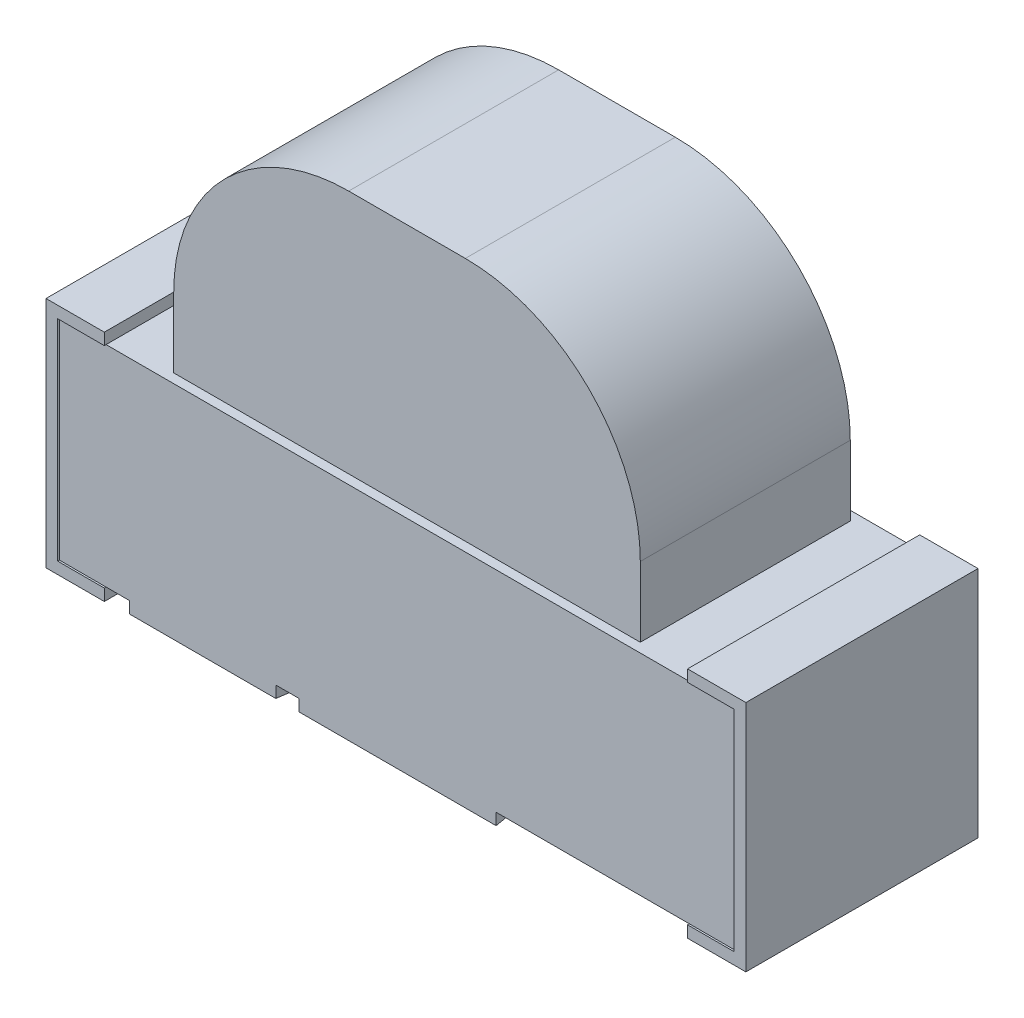
SolidWorks part; units mm, degrees
ref_plane "Vorne" through (0, 0, 0) normal (0, 0, 1) x (1, 0, 0)
ref_plane "Oben" through (0, 0, 0) normal (0, 1, 0) x (1, 0, 0)
ref_plane "Rechts" through (0, 0, 0) normal (1, 0, 0) x (0, 0, -1)
sketch "Skizze1" plane through (0, 0, 0) normal (0, 1, 0) x (1, 0, 0)
  line L0 (-1.45, -0.49) -> (1.45, 0.49) construction
  line L1 (-1.45, 0.49) -> (1.45, 0.49)
  line L2 (-1.45, 0.49) -> (-1.45, -0.49)
  line L3 (-1.45, -0.49) -> (1.45, -0.49)
  line L4 (1.45, 0.49) -> (1.45, -0.49)
  line L5 (1.45, -0.49) -> (-1.45, 0.49) construction
  dimension "D1" = 0.98
  dimension "D2" = 2.9
extrude "Linear austragen1" add sketch "Skizze1" along normal blind 0.9
sketch "Skizze2" plane through (0, 0, 0) normal (0, 0, 1) x (1, 0, 0)
  line L0 (-1.45, 0.9) -> (1.45, 0.9) construction
  line L1 (-1, 0.9) -> (1, 0.9)
  line L2 (-1, 0.9) -> (-1, 1.2)
  line L3 (-0.25, 1.95) -> (0.25, 1.95)
  line L4 (1, 0.9) -> (1, 1.2)
  line L7 (0, 0) -> (0, 0.9) construction
  arc A0 (0.25, 1.95) -> (1, 1.2) centre (0.25, 1.2) cw
  arc A1 (-1, 1.2) -> (-0.25, 1.95) centre (-0.25, 1.2) cw
  point P11 (1, 1.95)
  point P14 (-1, 1.95)
  dimension "D3" = 0.75
  dimension "D1" = 1.05
  dimension "D2" = 2
extrude "Linear austragen2" add sketch "Skizze2" against normal mid plane 0.9 separate body
sketch "Skizze5" plane through (0, 0.9, 0) normal (0, 1, 0) x (1, 0, 0)
  line L10 (-1.45, 0.49) -> (-1.45, -0.49) construction
  line L11 (-1.45, -0.49) -> (1.45, -0.49) construction
  line L12 (1.45, -0.49) -> (1.45, 0.49) construction
  line L13 (1.45, 0.49) -> (-1.45, 0.49) construction
  line L14 (-1.5, 0.54) -> (-1.5, -0.54)
  line L15 (-1.5, -0.54) -> (1.5, -0.54)
  line L16 (1.5, -0.54) -> (1.5, 0.54)
  line L17 (1.5, 0.54) -> (-1.5, 0.54)
  line L18 (-1.5, 0.54) -> (-1.5, -0.54)
  line L19 (-1.5, -0.54) -> (1.5, -0.54)
  line L20 (1.5, -0.54) -> (1.5, 0.54)
  line L21 (1.5, 0.54) -> (-1.5, 0.54)
  line L22 (-1.45, 0.49) -> (-1.45, -0.49)
  line L23 (-1.45, -0.49) -> (1.45, -0.49)
  line L24 (1.45, -0.49) -> (1.45, 0.49)
  line L25 (1.45, 0.49) -> (-1.45, 0.49)
  dimension "D1" = 0.05
extrude "Linear austragen6" add sketch "Skizze5" against normal up to surface (0.9 mm away) separate body up to face at (0, 0, 0)
sketch "Skizze6" plane through (0, 0.9, 0) normal (0, 1, 0) x (1, 0, 0)
  line L0 (1.5, -0.54) -> (-1.5, -0.54) construction
  line L1 (1.25, 0.54) -> (1.25, -0.54)
  line L2 (1.5, 0.54) -> (-1.5, 0.54) construction
  line L5 (-1.5, -0.54) -> (1.5, -0.54) construction
  line L6 (1.25, -0.54) -> (1.5, -0.54)
  line L7 (0, -0.54) -> (0, 0) construction
  line L8 (1.5, -0.54) -> (1.5, 0.54)
  line L9 (1.5, 0.54) -> (1.25, 0.54)
  line L10 (-1.5, 0.54) -> (-1.25, 0.54)
  line L11 (-1.5, -0.54) -> (-1.5, 0.54)
  line L12 (-1.25, -0.54) -> (-1.5, -0.54)
  line L13 (-1.25, 0.54) -> (-1.25, -0.54)
  dimension "D1" = 0.25
extrude "Linear austragen7" add sketch "Skizze6" along normal blind 0.05
sketch "Skizze7" plane through (0, 0, 0) normal (0, -1, 0) x (1, 0, 0)
  line L0 (1.5, -0.54) -> (1.25, -0.54) construction
  line L1 (1.5, 0.54) -> (1.5, -0.54) construction
  line L2 (1.25, 0.54) -> (1.5, 0.54) construction
  line L3 (1.25, -0.54) -> (1.25, 0.54) construction
  line L4 (1.5, -0.54) -> (1.25, -0.54)
  line L5 (1.5, 0.54) -> (1.5, -0.54)
  line L6 (1.25, 0.54) -> (1.5, 0.54)
  line L7 (1.25, -0.54) -> (1.25, 0.54)
  line L8 (0, 0) -> (0, 0.54) construction
  line L9 (1.5, 0.54) -> (-1.5, 0.54) construction
  line L10 (-1.25, -0.54) -> (-1.25, 0.54)
  line L11 (-1.25, 0.54) -> (-1.5, 0.54)
  line L12 (-1.5, 0.54) -> (-1.5, -0.54)
  line L13 (-1.5, -0.54) -> (-1.25, -0.54)
extrude "Linear austragen8" add sketch "Skizze7" along normal blind 0.05
sketch "Skizze8" plane through (0, 0, 0) normal (0, -1, 0) x (1, 0, 0)
  line L0 (0, 0.54) -> (0, -0.54) construction
  line L1 (1.25, 0.54) -> (-1.25, 0.54) construction
  line L2 (-1.25, -0.54) -> (1.25, -0.54) construction
  line L3 (0, 0) -> (1.5, 0) construction
  line L4 (1.5, -0.54) -> (1.5, 0.54) construction
  line L5 (-0.125, 0.1338) -> (-0.125, -0.1338)
  line L6 (0.125, 0.1338) -> (0.125, -0.1338)
  line L7 (-0.425, 0.54) -> (0.425, 0.54)
  line L8 (0.425, -0.54) -> (-0.425, -0.54)
  line L9 (-0.225, 0.0657) -> (-0.225, -0.0657)
  line L11 (-1.15, 0.54) -> (-0.525, 0.54)
  line L12 (-1.15, -0.54) -> (-1.15, 0.54)
  line L13 (-1.15, -0.54) -> (-1.15, 0.54)
  line L14 (-0.525, -0.54) -> (-1.15, -0.54)
  arc A0 (-0.425, 0.54) -> (-0.125, 0.1338) centre (0, 0.54) ccw
  arc A1 (-0.425, -0.54) -> (-0.125, -0.1338) centre (0, -0.54) cw
  arc A2 (0.125, 0.1338) -> (0.425, 0.54) centre (0, 0.54) ccw
  arc A3 (0.125, -0.1338) -> (0.425, -0.54) centre (0, -0.54) cw
  arc A4 (-0.525, 0.54) -> (-0.225, 0.0657) centre (0, 0.54) ccw
  arc A5 (-0.525, -0.54) -> (-0.225, -0.0657) centre (0, -0.54) cw
  dimension "D1" = 0.85
  dimension "D2" = 0.25
  dimension "D3" = 0.1
  dimension "D4" = 0.1
extrude "Linear austragen9" add sketch "Skizze8" along normal blind 0.05
sketch "Skizze9" plane through (0, 0, 0.54) normal (0, 0, 1) x (1, 0, 0)
  line L0 (0, 0) -> (0, 0.9) construction
  line L1 (-1.25, 0.9) -> (1.25, 0.9) construction
  line L2 (-1.45, 0.45) -> (1.4496, 0.45) construction
  line L4 (-1.45, 0.9) -> (-1.45, 0)
  line L5 (1.4496, 0) -> (1.25, 0)
  line L6 (1.4496, 0.9) -> (1.4496, 0)
  line L7 (0, 0.85) -> (0, 0.05) construction
  line L8 (-1.5, 0.45) -> (1.5, 0.45) construction
  line L9 (-1.5, -0.05) -> (-1.5, 0.95) construction
  line L10 (1.5, 0.95) -> (1.5, -0.05) construction
  line L12 (1.4496, 0.9) -> (-1.45, 0.9)
  line L15 (1.25, 0) -> (1.25, -0.05)
  line L16 (1.25, -0.05) -> (-1.25, -0.05)
  line L17 (-1.25, -0.05) -> (-1.25, 0)
  line L18 (-1.25, 0) -> (-1.45, 0)
  dimension "D1" = 0.9
  dimension "D2" = 2.8996
extrude "Schnitt-Linear austragen2" cut sketch "Skizze9" against normal blind 0.05
mirror "Spiegeln1" about plane through (0, 0, 0) normal (0, 0, 1) of "Schnitt-Linear austragen2"
sketch "Skizze10" plane through (0, 0, 0.54) normal (0, 0, 1) x (1, 0, 0)
  line L1 (-1.5, 0.95) -> (1.5, 0.95)
  line L2 (-1.5, 0.95) -> (-1.5, -0.05)
  line L3 (-1.5, -0.05) -> (1.5, -0.05)
  line L4 (1.5, 0.95) -> (1.5, -0.05)
extrude "Schnitt-Linear austragen3" cut sketch "Skizze10" against normal blind 0.0425
mirror "Spiegeln2" about plane through (0, 0, 0) normal (0, 0, 1) of "Schnitt-Linear austragen3"
